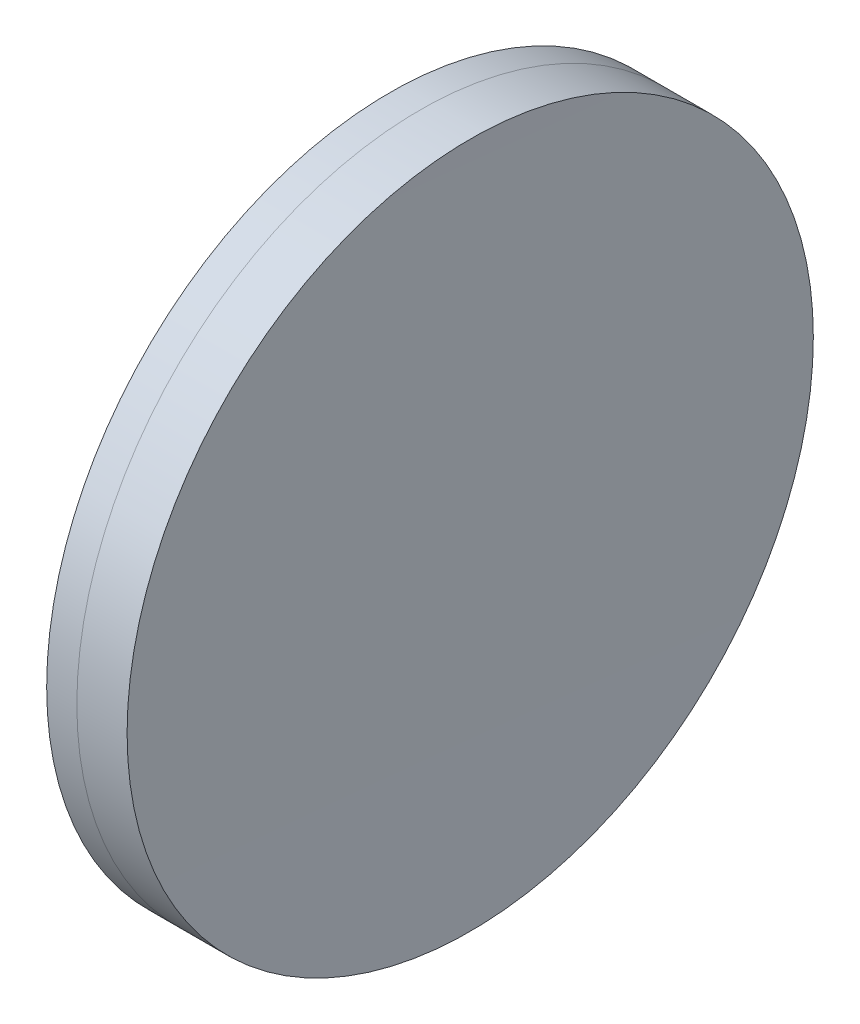
SolidWorks part; units mm, degrees
ref_plane "前视基准面" through (0, 0, 0) normal (0, 0, 1) x (1, 0, 0)
ref_plane "上视基准面" through (0, 0, 0) normal (0, 1, 0) x (1, 0, 0)
ref_plane "右视基准面" through (0, 0, 0) normal (1, 0, 0) x (0, 0, -1)
sketch "草图1" plane through (0, 0, 0) normal (0, 1, 0) x (1, 0, 0)
  line L0 (-402.0213, 0) -> (646.9917, 0) construction
  line L1 (-33.5938, -25.4) -> (-31.3612, -25.4)
  line L2 (-33.5938, 25.4) -> (-31.3612, 25.4)
  arc A0 (-31.3612, -25.4) -> (-31.3612, 25.4) centre (-321.3509, 0) ccw
  arc A1 (-33.5938, 25.4) -> (-33.5938, -25.4) centre (342.3491, 0) ccw
  point P10 (-34.4509, 0)
  point P11 (-30.2509, 0)
  dimension "D3" = 376.8
  dimension "D4" = 291.1
  dimension "D1" = 25.4
  dimension "D2" = 25.4
  dimension "D5" = 4.2
revolve "旋转1" add sketch "草图1" angle 360 about L0
sketch "草图2" plane through (0, 0, 0) normal (0, 1, 0) x (1, 0, 0)
  line L0 (-151.1285, 0) -> (622.6607, 0) construction
  line L2 (-31.3612, 25.4) -> (-27.6401, 25.4)
  line L3 (-31.3612, -25.4) -> (-27.6401, -25.4)
  arc A0 (-27.6401, 25.4) -> (-27.6401, -25.4) centre (2882.2491, 0) ccw
  arc A1 (-31.3612, -25.4) -> (-31.3612, 25.4) centre (-321.3509, 0) ccw construction
  arc A2 (-31.3612, -25.4) -> (-31.3612, 25.4) centre (-321.3509, 0) ccw
  point P4 (-30.2509, 0)
  point P8 (-27.7509, 0)
  dimension "D1" = 2910
  dimension "D2" = 2.5
revolve "旋转3" add sketch "草图2" angle 360 about L0
